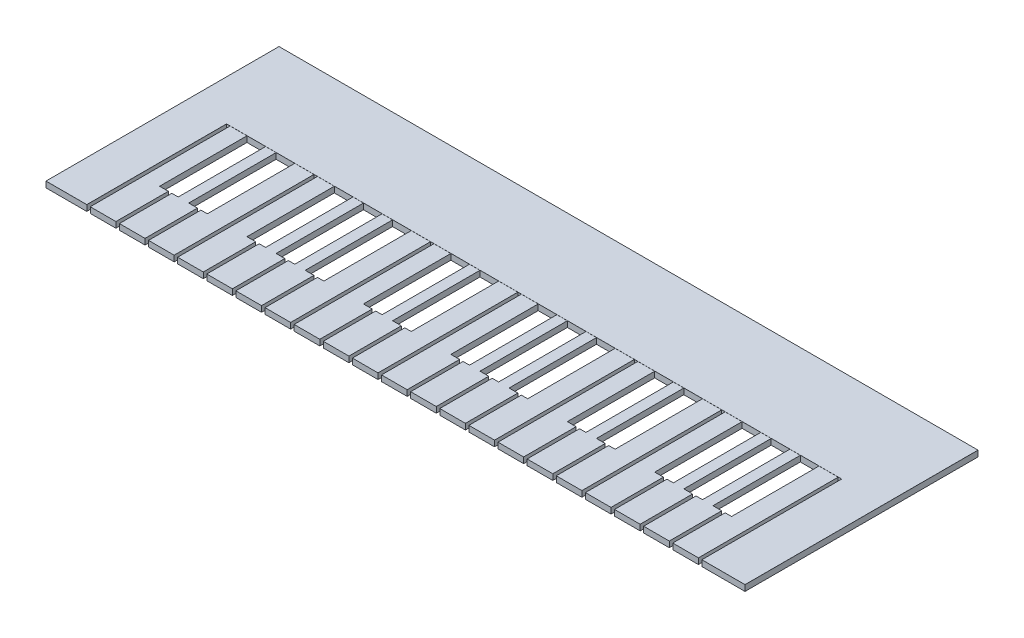
SolidWorks part; units mm, degrees
material "PVC 0.007 Plasticized"
ref_plane "Front Plane" through (0, 0, 0) normal (0, 0, 1) x (1, 0, 0)
ref_plane "Top Plane" through (0, 0, 0) normal (0, 1, 0) x (1, 0, 0)
ref_plane "Right Plane" through (0, 0, 0) normal (1, 0, 0) x (0, 0, -1)
sketch "Sketch1" plane through (0, 0, 0) normal (0, 1, 0) x (1, 0, 0)
  line L1 (0, 0) -> (600, 0)
  line L2 (0, 0) -> (0, 200)
  line L3 (0, 200) -> (600, 200)
  line L4 (600, 0) -> (600, 200)
  dimension "D1" = 600
  dimension "D2" = 200
extrude "Boss-Extrude1" add sketch "Sketch1" along normal blind 5
sketch "Sketch2" plane through (0, 5, 0) normal (0, 1, 0) x (1, 0, 0)
  line L0 (0, 0) -> (600, 0) construction
  line L1 (35, 0) -> (38, 0)
  line L2 (35, 0) -> (35, 120)
  line L3 (35, 120) -> (38, 120)
  line L4 (38, 0) -> (38, 120)
  line L5 (0, 200) -> (0, 0) construction
  line L6 (600, 200) -> (0, 200) construction
  line L7 (60, 0) -> (60, 120)
  line L8 (60, 0) -> (63, 0)
  line L9 (63, 0) -> (63, 120)
  line L10 (60, 120) -> (63, 120)
  line L11 (85, 0) -> (85, 120)
  line L12 (85, 0) -> (88, 0)
  line L13 (88, 0) -> (88, 120)
  line L14 (85, 120) -> (88, 120)
  line L15 (110, 0) -> (110, 120)
  line L16 (110, 0) -> (113, 0)
  line L17 (113, 0) -> (113, 120)
  line L18 (110, 120) -> (113, 120)
  line L19 (135, 0) -> (135, 120)
  line L20 (135, 0) -> (138, 0)
  line L21 (138, 0) -> (138, 120)
  line L22 (135, 120) -> (138, 120)
  line L23 (160, 0) -> (160, 120)
  line L24 (160, 0) -> (163, 0)
  line L25 (163, 0) -> (163, 120)
  line L26 (160, 120) -> (163, 120)
  line L27 (185, 0) -> (185, 120)
  line L28 (185, 0) -> (188, 0)
  line L29 (188, 0) -> (188, 120)
  line L30 (185, 120) -> (188, 120)
  line L31 (210, 0) -> (210, 120)
  line L32 (210, 0) -> (213, 0)
  line L33 (213, 0) -> (213, 120)
  line L34 (210, 120) -> (213, 120)
  line L35 (235, 0) -> (235, 120)
  line L36 (235, 0) -> (238, 0)
  line L37 (238, 0) -> (238, 120)
  line L38 (235, 120) -> (238, 120)
  line L39 (260, 0) -> (260, 120)
  line L40 (260, 0) -> (263, 0)
  line L41 (263, 0) -> (263, 120)
  line L42 (260, 120) -> (263, 120)
  line L43 (285, 0) -> (285, 120)
  line L44 (285, 0) -> (288, 0)
  line L45 (288, 0) -> (288, 120)
  line L46 (285, 120) -> (288, 120)
  line L47 (310, 0) -> (310, 120)
  line L48 (310, 0) -> (313, 0)
  line L49 (313, 0) -> (313, 120)
  line L50 (310, 120) -> (313, 120)
  line L51 (335, 0) -> (335, 120)
  line L52 (335, 0) -> (338, 0)
  line L53 (338, 0) -> (338, 120)
  line L54 (335, 120) -> (338, 120)
  line L55 (360, 0) -> (360, 120)
  line L56 (360, 0) -> (363, 0)
  line L57 (363, 0) -> (363, 120)
  line L58 (360, 120) -> (363, 120)
  line L59 (385, 0) -> (385, 120)
  line L60 (385, 0) -> (388, 0)
  line L61 (388, 0) -> (388, 120)
  line L62 (385, 120) -> (388, 120)
  line L63 (410, 0) -> (410, 120)
  line L64 (410, 0) -> (413, 0)
  line L65 (413, 0) -> (413, 120)
  line L66 (410, 120) -> (413, 120)
  line L67 (435, 0) -> (435, 120)
  line L68 (435, 0) -> (438, 0)
  line L69 (438, 0) -> (438, 120)
  line L70 (435, 120) -> (438, 120)
  line L71 (460, 0) -> (460, 120)
  line L72 (460, 0) -> (463, 0)
  line L73 (463, 0) -> (463, 120)
  line L74 (460, 120) -> (463, 120)
  line L75 (485, 0) -> (485, 120)
  line L76 (485, 0) -> (488, 0)
  line L77 (488, 0) -> (488, 120)
  line L78 (485, 120) -> (488, 120)
  line L79 (510, 0) -> (510, 120)
  line L80 (510, 0) -> (513, 0)
  line L81 (513, 0) -> (513, 120)
  line L82 (510, 120) -> (513, 120)
  line L83 (535, 0) -> (535, 120)
  line L84 (535, 0) -> (538, 0)
  line L85 (538, 0) -> (538, 120)
  line L86 (535, 120) -> (538, 120)
  line L87 (560, 0) -> (560, 120)
  line L88 (560, 0) -> (563, 0)
  line L89 (563, 0) -> (563, 120)
  line L90 (560, 120) -> (563, 120)
  dimension "D1" = 35
  dimension "D2" = 80
  dimension "D3" = 3
  dimension "D4" = 22
extrude "Cut-Extrude4" cut sketch "Sketch2" against normal blind 5
sketch "Sketch4" plane through (0, 5, 0) normal (0, 1, 0) x (1, 0, 0)
  line L0 (600, 200) -> (0, 200) construction
  line L1 (52.5, 120) -> (68.5, 120)
  line L2 (52.5, 120) -> (52.5, 45)
  line L3 (52.5, 45) -> (68.5, 45)
  line L4 (68.5, 120) -> (68.5, 45)
  line L5 (60, 120) -> (60, 0) construction
  line L6 (77.5, 120) -> (77.5, 45)
  line L7 (77.5, 120) -> (93.5, 120)
  line L8 (93.5, 120) -> (93.5, 45)
  line L9 (77.5, 45) -> (93.5, 45)
  line L10 (127.5, 120) -> (127.5, 45)
  line L11 (127.5, 45) -> (143.5, 45)
  line L12 (143.5, 120) -> (143.5, 45)
  line L13 (127.5, 120) -> (143.5, 120)
  line L14 (152.5, 120) -> (152.5, 45)
  line L15 (152.5, 45) -> (168.5, 45)
  line L16 (168.5, 120) -> (168.5, 45)
  line L17 (152.5, 120) -> (168.5, 120)
  line L18 (177.5, 120) -> (177.5, 45)
  line L19 (177.5, 45) -> (193.5, 45)
  line L20 (193.5, 120) -> (193.5, 45)
  line L21 (177.5, 120) -> (193.5, 120)
  line L22 (227.5, 120) -> (227.5, 45)
  line L23 (227.5, 120) -> (243.5, 120)
  line L24 (243.5, 120) -> (243.5, 45)
  line L25 (227.5, 45) -> (243.5, 45)
  line L26 (252.5, 120) -> (252.5, 45)
  line L27 (252.5, 45) -> (268.5, 45)
  line L28 (268.5, 120) -> (268.5, 45)
  line L29 (252.5, 120) -> (268.5, 120)
  line L30 (302.5, 120) -> (302.5, 45)
  line L31 (302.5, 45) -> (318.5, 45)
  line L32 (318.5, 120) -> (318.5, 45)
  line L33 (302.5, 120) -> (318.5, 120)
  line L34 (327.5, 120) -> (327.5, 45)
  line L35 (327.5, 45) -> (343.5, 45)
  line L36 (343.5, 120) -> (343.5, 45)
  line L37 (327.5, 120) -> (343.5, 120)
  line L38 (352.5, 120) -> (352.5, 45)
  line L39 (352.5, 45) -> (368.5, 45)
  line L40 (368.5, 120) -> (368.5, 45)
  line L41 (352.5, 120) -> (368.5, 120)
  line L42 (402.5, 120) -> (402.5, 45)
  line L43 (402.5, 120) -> (418.5, 120)
  line L44 (418.5, 120) -> (418.5, 45)
  line L45 (402.5, 45) -> (418.5, 45)
  line L46 (427.5, 120) -> (427.5, 45)
  line L47 (427.5, 45) -> (443.5, 45)
  line L48 (443.5, 120) -> (443.5, 45)
  line L49 (427.5, 120) -> (443.5, 120)
  line L50 (477.5, 120) -> (477.5, 45)
  line L51 (477.5, 45) -> (493.5, 45)
  line L52 (493.5, 120) -> (493.5, 45)
  line L53 (477.5, 120) -> (493.5, 120)
  line L54 (502.5, 120) -> (502.5, 45)
  line L55 (502.5, 45) -> (518.5, 45)
  line L56 (518.5, 120) -> (518.5, 45)
  line L57 (502.5, 120) -> (518.5, 120)
  line L58 (527.5, 120) -> (527.5, 45)
  line L59 (527.5, 45) -> (543.5, 45)
  line L60 (543.5, 120) -> (543.5, 45)
  line L61 (527.5, 120) -> (543.5, 120)
  point P6 (60.5, 45)
  dimension "D1" = 80
  dimension "D2" = 75
  dimension "D3" = 16
  dimension "D4" = 7.5
  dimension "D5" = 2
  dimension "D6" = 2
  dimension "D7" = 3
  dimension "D8" = 3
extrude "Cut-Extrude5" cut sketch "Sketch4" against normal blind 5
sketch "Sketch5" plane through (0, 5, 0) normal (0, 1, 0) x (1, 0, 0)
  line L1 (0, 0) -> (35, 0)
  line L2 (0, 0) -> (0, 120)
  line L4 (35, 0) -> (35, 120)
  line L6 (563, 120) -> (563, 0)
  line L7 (563, 0) -> (600, 0)
  line L8 (600, 120) -> (600, 0)
  line L9 (563, 120) -> (35, 120)
  line L10 (600, 120) -> (600, 200)
  line L11 (600, 200) -> (0, 200)
  line L12 (0, 120) -> (0, 200)
extrude "Boss-Extrude2" add sketch "Sketch5" along normal blind 0.1 separate body
